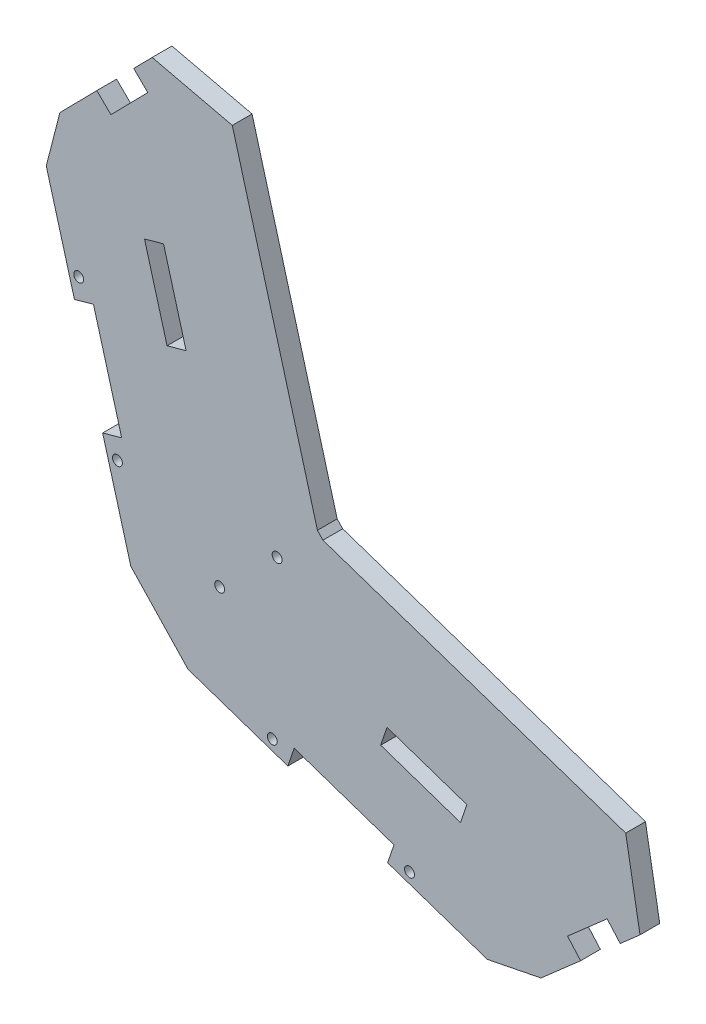
SolidWorks part; units mm, degrees
ref_plane "Alzado" through (0, 0, 0) normal (0, 0, 1) x (1, 0, 0)
ref_plane "Planta" through (0, 0, 0) normal (0, 1, 0) x (1, 0, 0)
ref_plane "Vista lateral" through (0, 0, 0) normal (1, 0, 0) x (0, 0, -1)
sketch "Croquis1" plane through (0, 0, 0) normal (0, 0, 1) x (1, 0, 0)
  line L9 (94.713, -28.6703) -> (124.7846, -2.2941)
  line L10 (124.7846, -2.2941) -> (121.4876, 1.4648)
  line L11 (5.4022, -5.6785) -> (81.1413, -31.3819)
  line L25 (-30.4895, 86.7174) -> (-9.0886, 9.652)
  line L36 (0.9872, 128.6602) -> (-27.0393, 100.1205)
  line L39 (4.5546, 125.1569) -> (0.9872, 128.6602)
  line L40 (-27.0393, 100.1205) -> (-30.4895, 86.7174)
  line L41 (-9.0886, 9.652) -> (5.4022, -5.6785)
  line L42 (81.1413, -31.3819) -> (94.713, -28.6703)
  line L43 (4.5546, 125.1569) -> (29.1628, 36.1106)
  line L44 (29.1628, 36.1106) -> (33.9713, 31.0235)
  line L45 (33.9713, 31.0235) -> (121.4876, 1.4648)
  dimension "D1" = 0.9872
  dimension "D2" = 4.5546
  dimension "D3" = 5.4022
  dimension "D4" = 29.1628
  dimension "D5" = 33.9713
  dimension "D6" = 81.1413
  dimension "D7" = 94.713
  dimension "D8" = 121.4876
  dimension "D9" = 124.7846
  dimension "D10" = 9.0886
  dimension "D11" = 27.0393
  dimension "D12" = 30.4895
  dimension "D13" = 1.4648
  dimension "D14" = 9.652
  dimension "D15" = 31.0235
  dimension "D16" = 36.1106
  dimension "D17" = 86.7174
  dimension "D18" = 100.1205
extrude "Saliente-Extruir1" add sketch "Croquis1" along normal blind 5
sketch "Croquis2" plane through (0, 0, 5) normal (0, 0, 1) x (1, 0, 0)
  line L0 (31.567, 33.5671) -> (-1.8432, 1.9868) construction
  line L1 (33.9713, 31.0235) -> (29.1628, 36.1106) construction
  line L2 (-9.0886, 9.652) -> (5.4022, -5.6785) construction
  circle A0 centre (27.9334, 30.1325) radius 1.25
  circle A1 centre (13.3988, 16.394) radius 1.25
  dimension "D1" = 2.5
  dimension "D2" = 2.5
  dimension "D3" = 20
  dimension "D4" = 5
extrude "Cortar-Extruir1" cut sketch "Croquis2" against normal blind 10
sketch "Croquis3" plane through (0, 0, 5) normal (0, 0, 1) x (1, 0, 0)
  line L0 (32.2612, -9.5135) -> (57.5133, -18.0832)
  line L1 (101.4399, -16.1193) -> (111.4637, -7.3272)
  line L2 (-11.4013, 36.6666) -> (-18.5366, 62.3609)
  line L3 (-14.1297, 106.1304) -> (-4.7875, 115.6436)
  line L4 (-30.4895, 86.7174) -> (-9.0886, 9.652) construction
  line L5 (0.9872, 128.6602) -> (-27.0393, 100.1205) construction
  line L6 (5.4022, -5.6785) -> (81.1413, -31.3819) construction
  line L7 (94.713, -28.6703) -> (124.7846, -2.2941) construction
  line L8 (-14.1297, 106.1304) -> (-17.6972, 109.6337)
  line L9 (-17.6972, 109.6337) -> (-8.355, 119.1469)
  line L10 (-8.355, 119.1469) -> (-4.7875, 115.6436)
  line L11 (-11.4013, 36.6666) -> (-16.219, 35.3287)
  line L12 (-18.5366, 62.3609) -> (-23.3543, 61.0231)
  line L13 (-23.3543, 61.0231) -> (-16.219, 35.3287)
  line L14 (32.2612, -9.5135) -> (30.6543, -14.2482)
  line L15 (30.6543, -14.2482) -> (55.9065, -22.818)
  line L16 (55.9065, -22.818) -> (57.5133, -18.0832)
  line L18 (111.4637, -7.3272) -> (114.7607, -11.0862)
  line L19 (114.7607, -11.0862) -> (104.7369, -19.8782)
  line L20 (101.4399, -16.1193) -> (104.7369, -19.8782)
  line L21 (4.5546, 125.1569) -> (0.9872, 128.6602) construction
  dimension "D1" = 5
  dimension "D2" = 5
  dimension "D3" = 5
  dimension "D4" = 5
  dimension "D5" = 13.3333
  dimension "D6" = 13.3333
  dimension "D7" = 26.6667
  dimension "D8" = 26.6667
  dimension "D9" = 26.6667
  dimension "D10" = 26.6667
  dimension "D11" = 13.3333
  dimension "D12" = 13.3333
extrude "Cortar-Extruir2" cut sketch "Croquis3" against normal blind 22
sketch "Croquis4" plane through (0, 0, 5) normal (0, 0, 1) x (1, 0, 0)
  line L0 (-11.3343, 103.6969) -> (5.7903, 42.0305)
  line L1 (5.7903, 42.0305) -> (10.608, 43.3683)
  line L2 (10.608, 43.3683) -> (-6.5166, 105.0347)
  line L3 (-6.5166, 105.0347) -> (-11.3343, 103.6969)
  line L4 (-30.4895, 86.7174) -> (-23.3543, 61.0231) construction
  line L5 (-18.5366, 62.3609) -> (-23.3543, 61.0231) construction
  line L7 (-5.6261, 83.1414) -> (-0.8084, 84.4793)
  line L8 (4.8998, 63.9238) -> (0.0821, 62.5859)
  line L9 (33.9423, 8.9243) -> (94.5474, -11.6431)
  line L10 (94.5474, -11.6431) -> (96.1542, -6.9084)
  line L11 (96.1542, -6.9084) -> (35.5491, 13.6591)
  line L12 (35.5491, 13.6591) -> (33.9423, 8.9243)
  line L14 (5.4022, -5.6785) -> (30.6543, -14.2482) construction
  line L15 (55.9065, -22.818) -> (57.5133, -18.0832) construction
  line L16 (55.7508, 6.8033) -> (54.144, 2.0685)
  line L17 (75.9525, -0.0525) -> (74.3457, -4.7873)
  dimension "D1" = 23
  dimension "D2" = 16.5683
  dimension "D3" = 64
  dimension "D4" = 5
  dimension "D5" = 21.3333
  dimension "D6" = 21.3333
  dimension "D7" = 5
  dimension "D8" = 23
  dimension "D9" = 64
  dimension "D10" = 33
  dimension "D11" = 21.3333
  dimension "D12" = 21.3333
extrude "Cortar-Extruir3" cut sketch "Croquis4" against normal blind 10 contours L8 L2 L7 L0 | L17 L11 L16 L9
sketch "Croquis5" plane through (0, 0, 5) normal (0, 0, 1) x (1, 0, 0)
  line L6 (4.5546, 125.1569) -> (9.374, 126.4887)
  line L7 (123.0875, 6.2019) -> (121.4876, 1.4648)
  line L8 (4.5546, 125.1569) -> (29.1628, 36.1106)
  line L9 (123.0875, 6.2019) -> (36.7501, 35.3624)
  line L10 (36.7501, 35.3624) -> (33.6508, 38.6413)
  line L11 (33.6508, 38.6413) -> (9.374, 126.4887)
  line L12 (123.0875, 6.2019) -> (36.7501, 35.3624)
  line L13 (36.7501, 35.3624) -> (33.6508, 38.6413)
  line L14 (33.6508, 38.6413) -> (9.374, 126.4887)
  line L15 (29.1628, 36.1106) -> (33.9713, 31.0235)
  line L16 (33.9713, 31.0235) -> (121.4876, 1.4648)
  dimension "D1" = 5
extrude "Saliente-Extruir2" add sketch "Croquis5" against normal blind 5
sketch "Croquis6" plane through (0, 0, 5) normal (0, 0, 1) x (1, 0, 0)
  line L0 (75.9525, -0.0525) -> (74.3457, -4.7873) construction
  line L1 (54.144, 2.0685) -> (74.3457, -4.7873) construction
  line L2 (75.9525, -0.0525) -> (55.7508, 6.8033) construction
  line L3 (55.7508, 6.8033) -> (54.144, 2.0685) construction
  line L4 (-5.6261, 83.1414) -> (-0.8084, 84.4793) construction
  line L5 (4.8998, 63.9238) -> (-0.8084, 84.4793) construction
  line L6 (-5.6261, 83.1414) -> (0.0821, 62.5859) construction
  line L7 (4.8998, 63.9238) -> (0.0821, 62.5859) construction
  line L8 (75.9525, -0.0525) -> (74.3457, -4.7873)
  line L9 (54.144, 2.0685) -> (74.3457, -4.7873)
  line L10 (75.9525, -0.0525) -> (55.7508, 6.8033)
  line L11 (55.7508, 6.8033) -> (54.144, 2.0685)
  line L12 (-5.6261, 83.1414) -> (-0.8084, 84.4793)
  line L13 (4.8998, 63.9238) -> (-0.8084, 84.4793)
  line L14 (-5.6261, 83.1414) -> (0.0821, 62.5859)
  line L15 (4.8998, 63.9238) -> (0.0821, 62.5859)
  line L30 (-4.7875, 115.6436) -> (-14.1297, 106.1304)
  line L31 (-14.1297, 106.1304) -> (-17.6972, 109.6337)
  line L32 (-17.6972, 109.6337) -> (-27.0393, 100.1205)
  line L33 (-27.0393, 100.1205) -> (-30.4895, 86.7174)
  line L34 (-30.4895, 86.7174) -> (-23.3543, 61.0231)
  line L35 (-23.3543, 61.0231) -> (-18.5366, 62.3609)
  line L36 (-18.5366, 62.3609) -> (-11.4013, 36.6666)
  line L37 (-11.4013, 36.6666) -> (-16.219, 35.3287)
  line L38 (-16.219, 35.3287) -> (-9.0886, 9.652)
  line L39 (-9.0886, 9.652) -> (5.4022, -5.6785)
  line L40 (5.4022, -5.6785) -> (30.6543, -14.2482)
  line L41 (30.6543, -14.2482) -> (32.2612, -9.5135)
  line L42 (32.2612, -9.5135) -> (57.5133, -18.0832)
  line L43 (57.5133, -18.0832) -> (55.9065, -22.818)
  line L44 (55.9065, -22.818) -> (81.1413, -31.3819)
  line L45 (81.1413, -31.3819) -> (94.713, -28.6703)
  line L46 (94.713, -28.6703) -> (104.7369, -19.8782)
  line L47 (104.7369, -19.8782) -> (101.4399, -16.1193)
  line L48 (101.4399, -16.1193) -> (111.4637, -7.3272)
  line L49 (111.4637, -7.3272) -> (114.7607, -11.0862)
  line L50 (114.7607, -11.0862) -> (124.7846, -2.2941)
  line L51 (124.7846, -2.2941) -> (121.4876, 1.4648)
  line L52 (121.4876, 1.4648) -> (123.0875, 6.2019)
  line L53 (123.0875, 6.2019) -> (36.7501, 35.3624)
  line L54 (36.7501, 35.3624) -> (33.6508, 38.6413)
  line L55 (33.6508, 38.6413) -> (9.374, 126.4887)
  line L56 (9.374, 126.4887) -> (4.5546, 125.1569)
  line L57 (4.5546, 125.1569) -> (0.9872, 128.6602)
  line L58 (0.9872, 128.6602) -> (-8.355, 119.1469)
  line L59 (-8.355, 119.1469) -> (-4.7875, 115.6436)
  line L60 (-4.7875, 115.6436) -> (-14.1297, 106.1304)
  line L61 (-14.1297, 106.1304) -> (-17.6972, 109.6337)
  line L62 (-17.6972, 109.6337) -> (-27.0393, 100.1205)
  line L63 (-27.0393, 100.1205) -> (-30.4895, 86.7174)
  line L64 (-30.4895, 86.7174) -> (-23.3543, 61.0231)
  line L65 (-23.3543, 61.0231) -> (-18.5366, 62.3609)
  line L66 (-18.5366, 62.3609) -> (-11.4013, 36.6666)
  line L67 (-11.4013, 36.6666) -> (-16.219, 35.3287)
  line L68 (-16.219, 35.3287) -> (-9.0886, 9.652)
  line L69 (-9.0886, 9.652) -> (5.4022, -5.6785)
  line L70 (5.4022, -5.6785) -> (30.6543, -14.2482)
  line L71 (30.6543, -14.2482) -> (32.2612, -9.5135)
  line L72 (32.2612, -9.5135) -> (57.5133, -18.0832)
  line L73 (57.5133, -18.0832) -> (55.9065, -22.818)
  line L74 (55.9065, -22.818) -> (81.1413, -31.3819)
  line L75 (81.1413, -31.3819) -> (94.713, -28.6703)
  line L76 (94.713, -28.6703) -> (104.7369, -19.8782)
  line L77 (104.7369, -19.8782) -> (101.4399, -16.1193)
  line L78 (101.4399, -16.1193) -> (111.4637, -7.3272)
  line L79 (111.4637, -7.3272) -> (114.7607, -11.0862)
  line L80 (114.7607, -11.0862) -> (124.7846, -2.2941)
  line L81 (124.7846, -2.2941) -> (121.4876, 1.4648)
  line L82 (121.4876, 1.4648) -> (123.0875, 6.2019)
  line L83 (123.0875, 6.2019) -> (36.7501, 35.3624)
  line L84 (36.7501, 35.3624) -> (33.6508, 38.6413)
  line L85 (33.6508, 38.6413) -> (9.374, 126.4887)
  line L86 (9.374, 126.4887) -> (4.5546, 125.1569)
  line L87 (4.5546, 125.1569) -> (0.9872, 128.6602)
  line L88 (0.9872, 128.6602) -> (-8.355, 119.1469)
  line L89 (-8.355, 119.1469) -> (-4.7875, 115.6436)
  circle A0 centre (13.3988, 16.394) radius 1.25 construction
  circle A1 centre (27.9334, 30.1325) radius 1.25 construction
  circle A2 centre (13.3988, 16.394) radius 1.25
  circle A3 centre (27.9334, 30.1325) radius 1.25
  dimension "D1" = 0
sketch "Croquis7" plane through (0, 0, 0) normal (0, 0, -1) x (-1, 0, 0)
  line L0 (-57.5133, -18.0832) -> (-55.9065, -22.818) construction
  line L1 (-55.9065, -22.818) -> (-81.1413, -31.3819) construction
  line L2 (-30.6543, -14.2482) -> (-32.2612, -9.5135) construction
  line L3 (-5.4022, -5.6785) -> (-30.6543, -14.2482) construction
  line L4 (11.4013, 36.6666) -> (16.219, 35.3287) construction
  line L5 (16.219, 35.3287) -> (9.0886, 9.652) construction
  line L6 (23.3543, 61.0231) -> (18.5366, 62.3609) construction
  line L7 (30.4895, 86.7174) -> (23.3543, 61.0231) construction
  circle A0 centre (-61.4447, -22.0575) radius 1.25
  circle A1 centre (-26.723, -10.274) radius 1.25
  circle A2 centre (12.4723, 31.18) radius 1.25
  circle A3 centre (22.2833, 66.5097) radius 1.25
  dimension "D1" = 2.5
  dimension "D2" = 5
  dimension "D3" = 2.5
  dimension "D4" = 5
  dimension "D5" = 2.5
  dimension "D6" = 5
  dimension "D7" = 2.5
  dimension "D8" = 5
  dimension "D9" = 2.5
extrude "Cortar-Extruir4" cut sketch "Croquis7" against normal blind 10
sketch "Croquis8" plane through (0, 0, 0) normal (0, 0, -1) x (-1, 0, 0)
  line L10 (-33.6508, 38.6413) -> (-9.374, 126.4887) construction
  line L11 (-36.7501, 35.3624) -> (-33.6508, 38.6413) construction
  line L12 (-123.0875, 6.2019) -> (-36.7501, 35.3624) construction
  line L21 (-33.6508, 38.6413) -> (-9.374, 126.4887)
  line L22 (-36.7501, 35.3624) -> (-33.6508, 38.6413)
  line L23 (-123.0875, 6.2019) -> (-36.7501, 35.3624)
  line L24 (-124.6875, 10.939) -> (-39.529, 39.7014)
  line L25 (-39.529, 39.7014) -> (-38.1389, 41.1721)
  line L26 (-38.1389, 41.1721) -> (-14.1934, 127.8206)
  line L27 (-123.0875, 6.2019) -> (-124.6875, 10.939)
  line L28 (-9.374, 126.4887) -> (-14.1934, 127.8206)
  dimension "D1" = 5
extrude "Saliente-Extruir3" add sketch "Croquis8" against normal blind 5
sketch "Croquis9" plane through (0, 0, 0) normal (0, 0, -1) x (-1, 0, 0)
  line L0 (-119.7726, -6.6901) -> (-116.1607, 13.819)
  line L1 (-114.7607, -11.0862) -> (-124.7846, -2.2941) construction
  line L2 (-39.529, 39.7014) -> (-124.6875, 10.939) construction
  line L3 (-121.4876, 1.4648) -> (-124.6875, 10.939) construction
  line L4 (-124.7846, -2.2941) -> (-121.4876, 1.4648) construction
  line L5 (-116.1607, 13.819) -> (-124.6875, 10.939)
  line L6 (-121.4876, 1.4648) -> (-124.6875, 10.939)
  line L7 (-124.7846, -2.2941) -> (-121.4876, 1.4648)
  line L8 (-119.7726, -6.6901) -> (-124.7846, -2.2941)
  line L9 (3.6839, 123.9036) -> (-16.5907, 119.1457)
  line L10 (-0.9872, 128.6602) -> (8.355, 119.1469) construction
  line L11 (-14.1934, 127.8206) -> (-38.1389, 41.1721) construction
  line L12 (-14.1934, 127.8206) -> (-4.5546, 125.1569) construction
  line L13 (-4.5546, 125.1569) -> (-0.9872, 128.6602) construction
  line L14 (-14.1934, 127.8206) -> (-16.5907, 119.1457)
  line L15 (-14.1934, 127.8206) -> (-4.5546, 125.1569)
  line L16 (-4.5546, 125.1569) -> (-0.9872, 128.6602)
  line L17 (-0.9872, 128.6602) -> (3.6839, 123.9036)
  dimension "D1" = 9
  dimension "D2" = 9
extrude "Cortar-Extruir7" cut sketch "Croquis9" against normal blind 10
